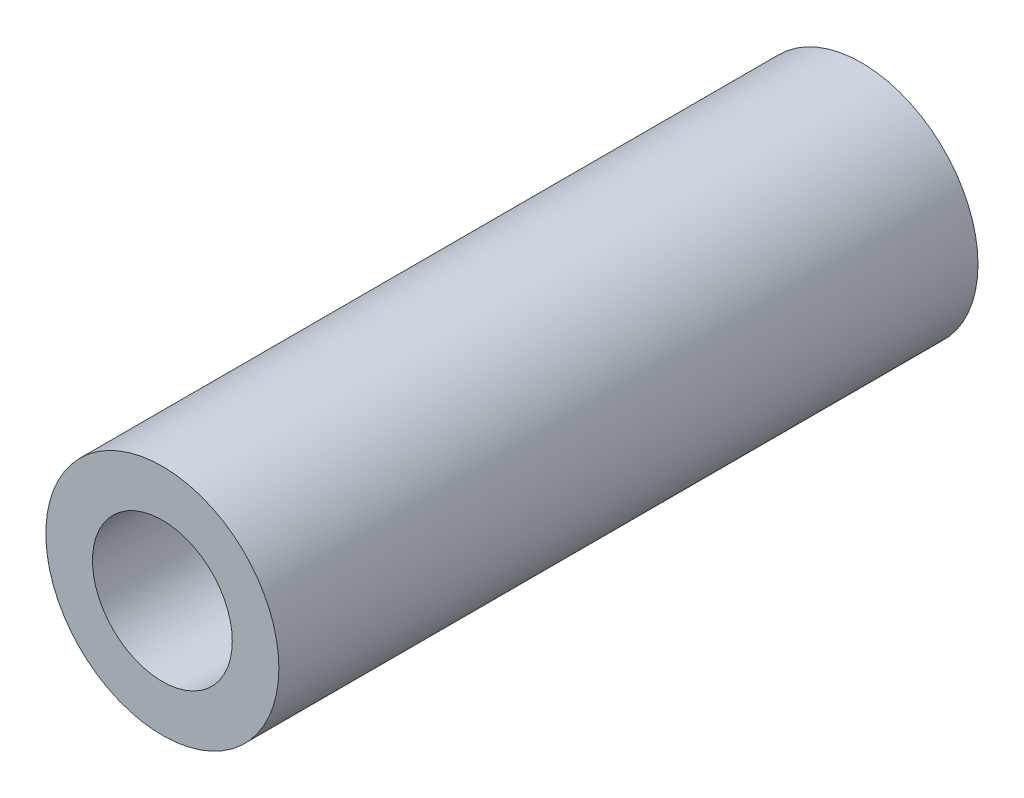
SolidWorks part; units mm, degrees
material "18-8 Stainless"
ref_plane "Front Plane" through (0, 0, 0) normal (0, 0, 1) x (1, 0, 0)
ref_plane "Top Plane" through (0, 0, 0) normal (0, 1, 0) x (1, 0, 0)
ref_plane "Right Plane" through (0, 0, 0) normal (1, 0, 0) x (0, 0, -1)
sketch "Sketch1" plane through (0, 0, 0) normal (0, 0, 1) x (1, 0, 0)
  circle A0 centre (0, 0) radius 7.9375
  circle A1 centre (0, 0) radius 3.2004
  dimension "OD" = 15.875
  dimension "ID" = 6.4008
extrude "Extrude1" add sketch "Sketch1" along normal mid plane 50.8
sketch "Sketch2" plane through (0, 0, 0) normal (1, 0, 0) x (0, 0, -1)
  line L0 (-25.4, -3.2004) -> (25.4, -3.2004) construction
  line L3 (25.4, 3.2004) -> (-25.4, 3.2004) construction
  line L5 (-25.4, -3.2004) -> (25.4, -3.2004)
  line L6 (25.4, 3.2004) -> (-25.4, 3.2004)
sketch "Sketch4" plane through (0, 0, 25.4) normal (0, 0, 1) x (1, 0, 0)
  line L0 (0, 0) -> (-2.263, 2.263)
  line L1 (0, -2.1828) -> (0, 2.1828) construction
  circle A0 centre (0, 0) radius 3.2004 construction
  dimension "D1" = 45
sketch "Sketch5" plane through (0, 0, 25.4) normal (0, 0, 1) x (1, 0, 0)
  circle A0 centre (0, 0) radius 3.2004 construction
  circle A1 centre (0, 0) radius 7.9375
  circle A2 centre (0, 0) radius 7.9375
  circle A3 centre (0, 0) radius 3.2004
  dimension "D1" = 0
extrude "Cut-Extrude1" cut sketch "Sketch5" against normal blind 3.175
sketch "Sketch6" plane through (0, 0, 22.225) normal (0, 0, 1) x (1, 0, 0)
  circle A0 centre (0, 0) radius 4.7625
  dimension "D1" = 9.525
extrude "Cut-Extrude2" cut sketch "Sketch6" against normal through all
